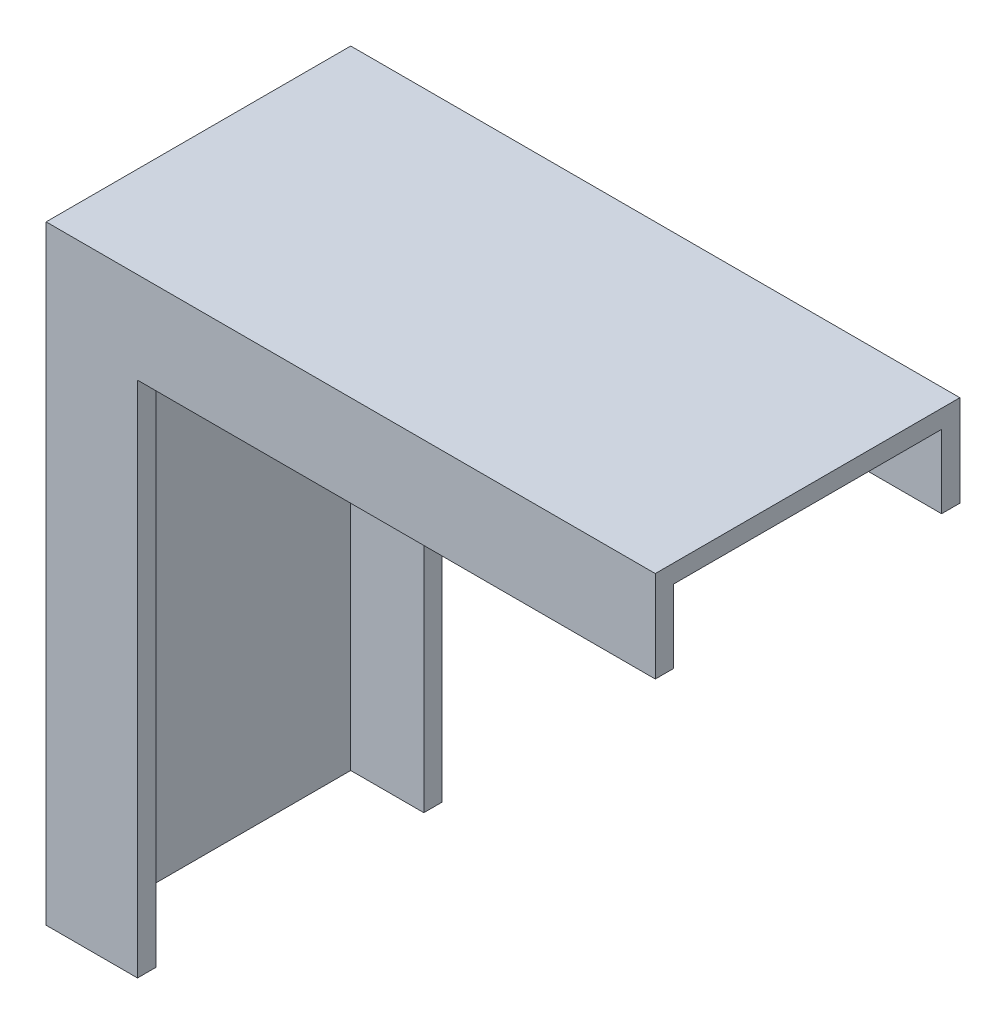
SolidWorks part; units mm, degrees
ref_plane "Ebene vorne" through (0, 0, 0) normal (0, 0, 1) x (1, 0, 0)
ref_plane "Ebene oben" through (0, 0, 0) normal (0, 1, 0) x (1, 0, 0)
ref_plane "Ebene rechts" through (0, 0, 0) normal (1, 0, 0) x (0, 0, -1)
sketch "Skizze1" plane through (0, 0, 0) normal (0, 0, 1) x (1, 0, 0)
  line L0 (0, 0) -> (0, 100)
  line L1 (0, 100) -> (100, 100)
  dimension "D1" = 100
  dimension "D2" = 100
extrude "Linear-Austragen-Dünn1" add sketch "Skizze1" along normal blind 50 thin
sketch "Skizze3" plane through (100, 0, 0) normal (1, 0, 0) x (0, 0, -1)
  line L0 (-50, 100) -> (0, 100) construction
  line L1 (-47, 97) -> (-3, 97)
  line L2 (-47, 97) -> (-47, -3.6664)
  line L3 (-47, -3.6664) -> (-3, -3.6664)
  line L4 (-3, 97) -> (-3, -3.6664)
  line L5 (-50, 100) -> (-50, 85) construction
  line L6 (0, 100) -> (0, 85) construction
  dimension "D1" = 3
  dimension "D2" = 3
  dimension "D3" = 3
extrude "Schnitt-Linear austragen2" cut sketch "Skizze3" against normal blind 97
